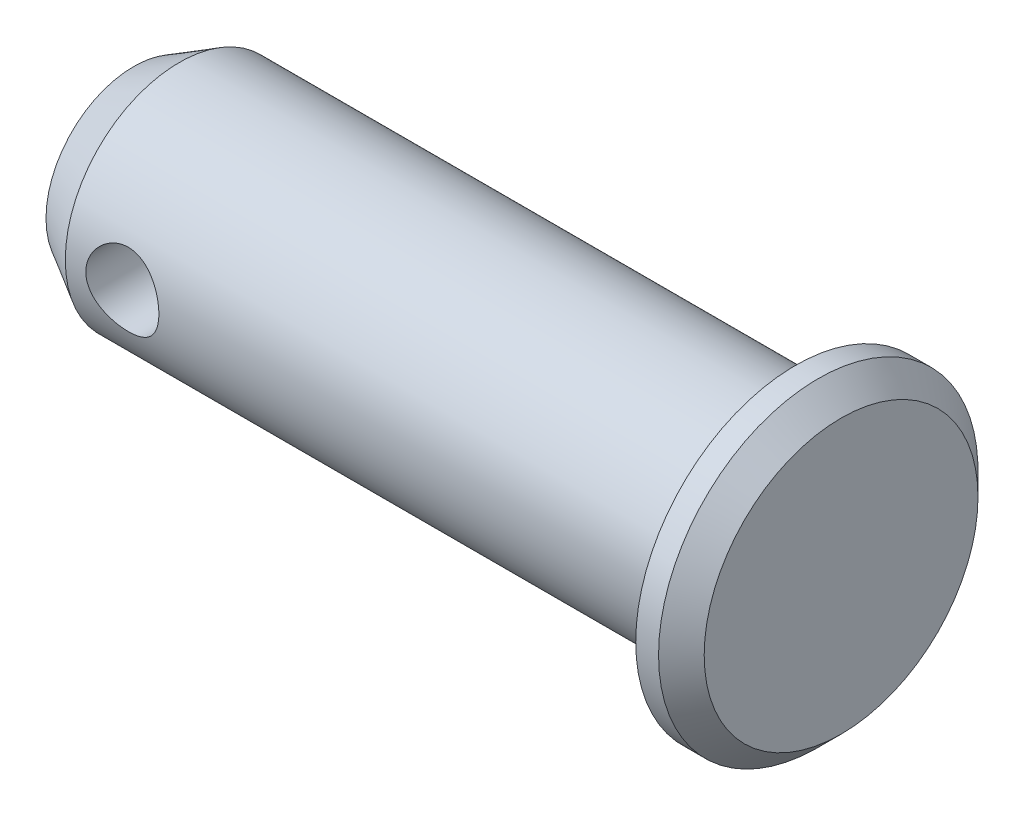
SolidWorks part; units mm, degrees
material "Plain Carbon Steel"
ref_plane "Front" through (0, 0, 0) normal (0, 0, 1) x (1, 0, 0)
ref_plane "Top" through (0, 0, 0) normal (0, 1, 0) x (1, 0, 0)
ref_plane "Right" through (0, 0, 0) normal (1, 0, 0) x (0, 0, -1)
sketch "Sketch1" plane through (0, 0, 0) normal (0, 0, 1) x (1, 0, 0)
  line L0 (0, 0) -> (-74.8754, 0) construction
  line L1 (0, 0) -> (-29, 0)
  line L2 (0, 0) -> (0, 5)
  line L3 (0, 5) -> (-29, 5)
  line L4 (-29, 0) -> (-29, 5)
  dimension "BOSS LENGTH" = 29
  dimension "BOSS DIA" = 10
revolve "Body Revolve" add sketch "Sketch1" angle 360 about L0
sketch "Sketch14" plane through (0, 0, 0) normal (0, 0, 1) x (1, 0, 0)
  line L0 (0, -5) -> (0, 5) construction
  line L1 (0, 0) -> (2, 0)
  line L2 (0, 0) -> (0, 7)
  line L3 (0, 7) -> (1, 7)
  line L4 (2, 0) -> (2, 6)
  line L5 (0, 0) -> (3.8052, 0) construction
  line L6 (1, 7) -> (2, 6)
  point P1 (2, 7)
  dimension "D1" = 14
  dimension "D2" = 2
revolve "Head Revolve" add sketch "Sketch14" angle 360 about L5
chamfer "Head Chamfer" distance 2 angle 30 1 edges at (-29, 0, -5)
sketch "Sketch21" plane through (0, 0, 0) normal (0, 0, 1) x (1, 0, 0)
  line L0 (0, 0) -> (-24.5, 0) construction
  circle A0 centre (-24.5, 0) radius 1.6
  dimension "D1" = 24.5
  dimension "D2" = 3.2
extrude "R Clip Hole" cut sketch "Sketch21" against normal through all both and the other way through all
